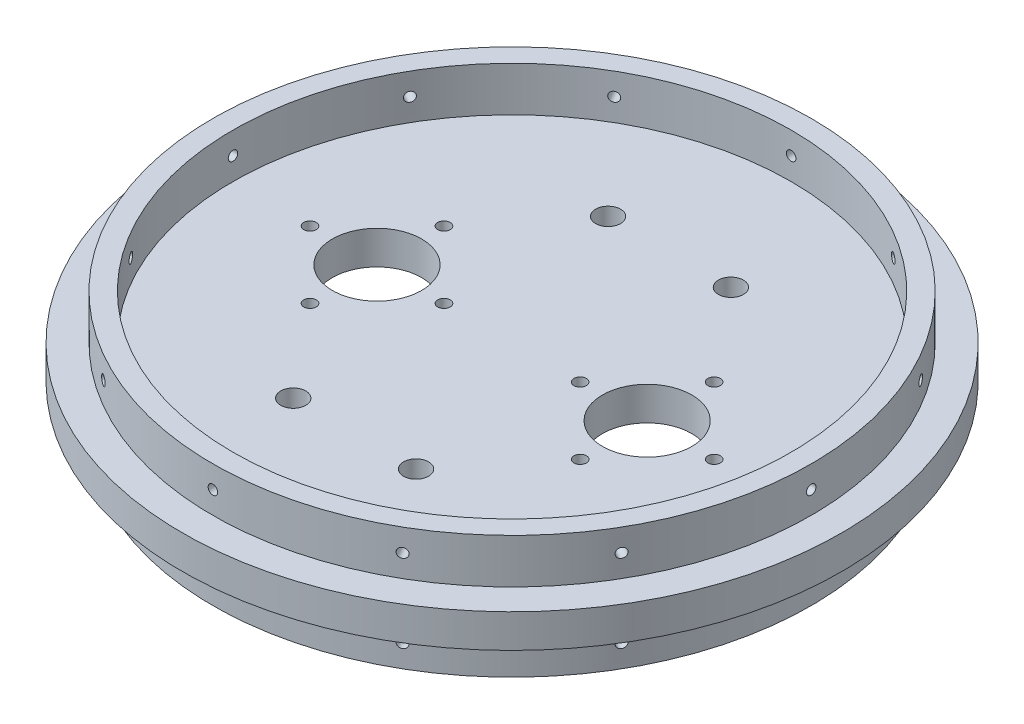
SolidWorks part; units mm, degrees
material "6061-T6 (SS)"
ref_plane "Front Plane" through (0, 0, 0) normal (0, 0, 1) x (1, 0, 0)
ref_plane "Top Plane" through (0, 0, 0) normal (0, 1, 0) x (1, 0, 0)
ref_plane "Right Plane" through (0, 0, 0) normal (1, 0, 0) x (0, 0, -1)
sketch "Sketch1" plane through (0, 0, 0) normal (0, 1, 0) x (1, 0, 0)
  line L5 (0, 0) -> (127.635, 0)
  line L6 (0, 0) -> (0, 127.635)
  line L7 (0, 127.635) -> (127.635, 127.635)
  line L8 (127.635, 0) -> (127.635, 127.635)
  dimension "D1" = 127.635
  dimension "D2" = 127.635
extrude "Boss-Extrude1" add sketch "Sketch1" along normal blind 9.525 contours L5 L8 L7 L6
sketch "Sketch12" plane through (0, 0, 0) normal (0, -1, 0) x (1, 0, 0)
  line L0 (63.8175, 0) -> (63.8175, -127.635) construction
  line L1 (0, 0) -> (127.635, 0) construction
  line L2 (0, -127.635) -> (127.635, -127.635) construction
  line L3 (0, -63.8175) -> (127.635, -63.8175) construction
  line L4 (0, 0) -> (0, -127.635) construction
  line L5 (127.635, 0) -> (127.635, -127.635) construction
  circle A0 centre (63.8175, -63.8175) radius 93.726
  dimension "D1" = 187.452
extrude "Boss-Extrude2" add sketch "Sketch12" against normal up to surface (9.525 mm away) contours A0 up to face at (63.8175, 9.525, -63.8175)
sketch "Sketch5" plane through (0, 9.525, 0) normal (0, 1, 0) x (1, 0, 0)
  circle A0 centre (63.8175, 63.8175) radius 46.355
  circle A3 centre (63.8175, 63.8175) radius 93.726 construction
  point P2 (0, 0)
  dimension "D1" = 92.71
ref_plane "Support mirror reference plane" through (0, 4.7625, 0) normal (0, 1, 0) x (1, 0, 0)
sketch "Sketch30" plane through (0, 0, 0) normal (0, -1, 0) x (1, 0, 0)
  circle A0 centre (63.8175, -63.8175) radius 85.09
  circle A1 centre (63.8175, -63.8175) radius 79.375
  dimension "D1" = 170.18
  dimension "D2" = 158.75
extrude "Boss-Extrude3" add sketch "Sketch30" along normal blind 12.7
mirror "Mirror1" about plane through (0, 4.7625, 0) normal (0, 1, 0) of "Boss-Extrude3"
sketch "Sketch31" plane through (0, 0, 0) normal (0, -1, 0) x (-1, 0, 0)
  line L0 (-63.8175, -52.481) -> (-63.8175, 177.7216) construction
ref_plane "Plane1" through (0, 0, -148.9075) normal (0, 0, -1) x (-1, 0, 0)
ref_plane "Plane2" through (63.8175, 0, 0) normal (-1, 0, 0) x (0, 0, -1)
sketch "Sketch32" plane through (0, 0, -148.9075) normal (0, 0, -1) x (-1, 0, 0)
  line L4 (-63.8175, -87.3125) -> (-63.8175, 87.3125) construction
  line L5 (-148.9075, 0) -> (21.2725, 0) construction
  line L6 (21.2725, 9.525) -> (-148.9075, 9.525) construction
  circle A0 centre (-63.8175, -6.35) radius 1.3526
  circle A1 centre (-63.8175, 15.875) radius 1.3525
  dimension "D1" = 2.7051
  dimension "D2" = 2.7051
  dimension "D3" = 6.35
  dimension "D4" = 6.35
extrude "Cut-Extrude4" cut sketch "Sketch32" against normal blind 15.24
pattern_circular "CirPattern2" count 12 over 360 about axis through (63.8175, -12.7, -63.8175) along (0, 1, 0) of "Cut-Extrude4"
ref_plane "Plane3" through (0, 0, -63.8175) normal (0, 0, 1) x (1, 0, 0)
sketch "Sketch35" plane through (0, 0, 0) normal (0, -1, 0) x (1, 0, 0)
  line L0 (71.3144, -63.8175) -> (-71.3144, -63.8175) construction
  line L3 (25.4, -63.8175) -> (25.4, -40.3618) construction
  line L4 (63.8175, 87.3125) -> (63.8175, -87.3125) construction
  circle A0 centre (25.4, -63.8175) radius 12.7
  circle A1 centre (25.4, -44.7675) radius 1.778
  circle A2 centre (44.45, -63.8175) radius 1.778
  circle A3 centre (25.4, -82.8675) radius 1.778
  circle A4 centre (6.35, -63.8175) radius 1.778
  circle A5 centre (102.235, -44.7675) radius 1.778
  circle A6 centre (83.185, -63.8175) radius 1.778
  circle A7 centre (102.235, -82.8675) radius 1.778
  circle A8 centre (121.285, -63.8175) radius 1.778
  circle A9 centre (102.235, -63.8175) radius 12.7
  point P9 (25.7981, -63.8175)
  point P10 (25.7981, -63.8175)
  point P15 (25.4, -63.8175)
  point P19 (25.4, -63.8175)
  point P25 (25.4, -63.8175)
  dimension "D1" = 3.556
  dimension "D4" = 25.4
  dimension "D5" = 76.835
  dimension "D2" = 19.05
  dimension "D3" = 4
extrude "Co2 mounts" cut sketch "Sketch35" against normal through all
sketch "Sketch36" plane through (0, 0, 0) normal (0, -1, 0) x (1, 0, 0)
  line L0 (63.8175, 87.3125) -> (63.8175, -87.3125) construction
  line L1 (71.3144, -63.8175) -> (-71.3144, -63.8175) construction
  circle A0 centre (81.28, -108.585) radius 3.556
  circle A1 centre (46.355, -108.585) radius 3.556
  circle A2 centre (46.355, -19.05) radius 3.556
  circle A3 centre (81.28, -19.05) radius 3.556
  dimension "D1" = 7.112
  dimension "D3" = 89.535
  dimension "D2" = 34.925
extrude "U bolt mounts" cut sketch "Sketch36" against normal through all
